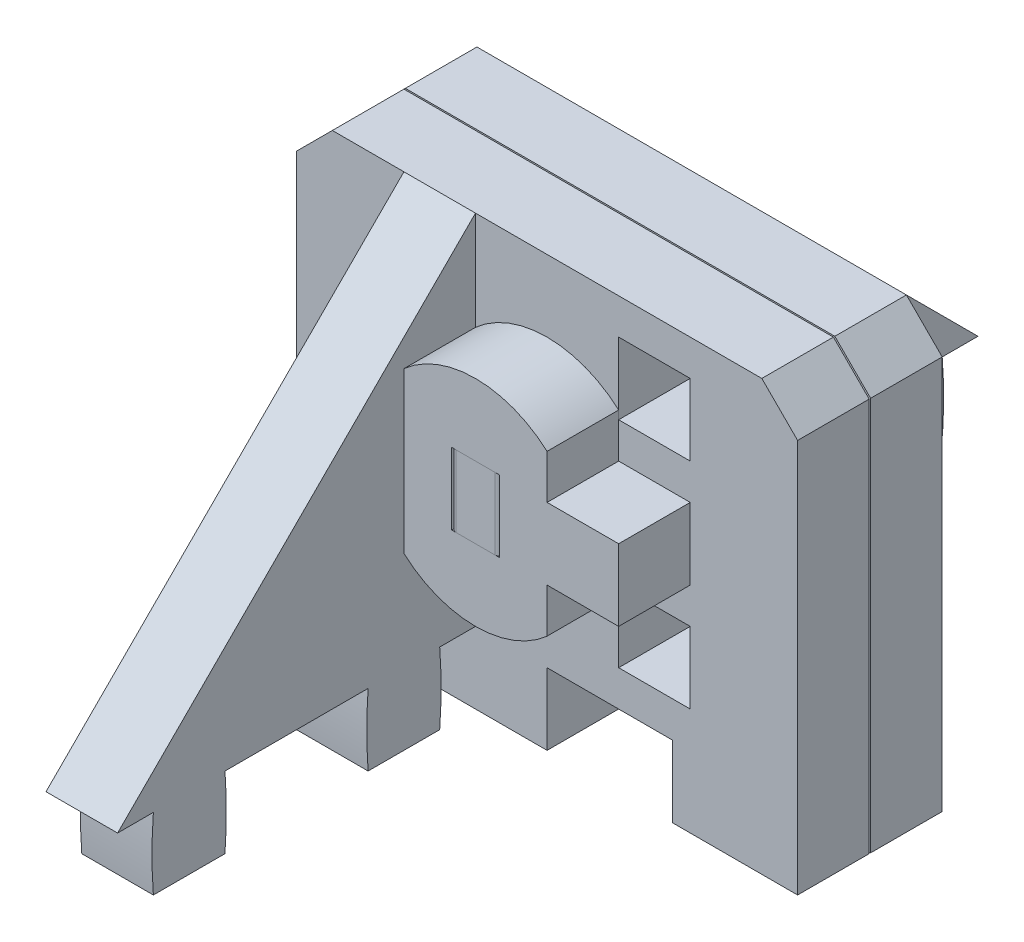
SolidWorks part; units mm, degrees
material "Faggio"
ref_plane "Piano frontale" through (0, 0, 0) normal (0, 0, 1) x (1, 0, 0)
ref_plane "Piano superiore" through (0, 0, 0) normal (0, 1, 0) x (1, 0, 0)
ref_plane "Piano destro" through (0, 0, 0) normal (1, 0, 0) x (0, 0, -1)
sketch "Schizzo1" plane through (0, 0, 0) normal (0, 0, 1) x (1, 0, 0)
  line L0 (-6, 6) -> (-6, 3)
  line L1 (-6, 3) -> (-3, 3)
  line L2 (-3, 3) -> (-3, 6)
  line L3 (-3, 6) -> (-6, 6)
  line L4 (-3, 3) -> (3, 3) construction
  line L5 (-6, -3) -> (-3, -3)
  line L6 (-6, -3) -> (-6, -6)
  line L7 (-6, -6) -> (-3, -6)
  line L8 (-3, -3) -> (-3, -6)
  line L17 (-1.5, -1.5) -> (1.5, -1.5) construction
  line L18 (-1.5, -1.5) -> (-1.5, 1.5) construction
  line L19 (-1.5, 1.5) -> (1.5, 1.5) construction
  line L20 (1.5, -1.5) -> (1.5, 1.5) construction
  line L21 (3, -3) -> (3, -6)
  line L22 (-10.5, 10.5) -> (-10.5, -10.5)
  line L23 (-10.5, -10.5) -> (10.5, -10.5)
  line L24 (10.5, -10.5) -> (10.5, 10.5)
  line L25 (10.5, 10.5) -> (-10.5, 10.5)
  line L26 (0, 10.5) -> (0, -10.5) construction
  line L27 (6, -6) -> (3, -6)
  line L28 (6, -3) -> (6, -6)
  line L29 (6, -3) -> (3, -3)
  line L30 (3, 6) -> (6, 6)
  line L31 (3, 3) -> (3, 6)
  line L32 (6, 3) -> (3, 3)
  line L33 (6, 6) -> (6, 3)
  line L35 (-3, 3) -> (-3, -3) construction
  circle A0 centre (0, 0) radius 2.1213
  point P30 (-3, 0)
extrude "Estrusione-Estrusione1" add sketch "Schizzo1" along normal blind 3
sketch "Schizzo6" plane through (0, 0, 3) normal (0, 0, 1) x (1, 0, 0)
  line L0 (-10.5, -7.5) -> (-5.25, -7.5)
  line L1 (-10.5, 10.5) -> (-10.5, -10.5) construction
  line L2 (-5.25, -7.5) -> (-5.25, -10.5)
  line L3 (-10.5, -10.5) -> (10.5, -10.5) construction
  line L4 (-5.25, -10.5) -> (0, -10.5) construction
  line L5 (0, -10.5) -> (0, -7.5)
  line L6 (0, -7.5) -> (5.25, -7.5)
  line L7 (5.25, -7.5) -> (5.25, -10.5)
  line L8 (5.25, -10.5) -> (0, -10.5)
  line L9 (-5.25, -10.5) -> (-10.5, -10.5)
  line L10 (-10.5, -10.5) -> (-10.5, -7.5)
  line L11 (5.25, -10.5) -> (10.5, -10.5) construction
  line L12 (10.5, -10.5) -> (10.5, 10.5) construction
extrude "Taglio-Estrusione1" cut sketch "Schizzo6" against normal up to next
sketch "Schizzo2" plane through (-6, 0, 0) normal (1, 0, 0) x (0, 0, -1)
  line L0 (-3, 6) -> (0, 6) construction
  line L1 (-3, 6) -> (0, 6) construction
  line L2 (-3, 6) -> (-3, 3) construction
  line L3 (0, 6) -> (0, 3) construction
  line L4 (-3, 6) -> (-3, 3)
  line L5 (-3, 3) -> (0, 3) construction
  line L6 (0, 10.5) -> (0, -7.5) construction
  line L7 (-3, 3) -> (0, 3) construction
  line L8 (0, 3) -> (0, 1.5)
  line L9 (0, -3) -> (-3, -3) construction
  line L10 (-3, -3) -> (-3, -6)
  line L11 (-3, -6) -> (0, -6) construction
  line L12 (0, -6) -> (0, -7.5)
  line L23 (15.75, -5.25) -> (2.25, 8.25)
  line L24 (2.25, 8.25) -> (0, 8.25)
  line L25 (0, 8.25) -> (0, 6)
  line L26 (0, -10.5) -> (0, 10.5) construction
  line L27 (0, -7.5) -> (9, 1.5) construction
  line L28 (15.75, -7.5) -> (13.5, -7.5)
  line L29 (15.75, -5.25) -> (15.75, -7.5)
  line L30 (1.5, -7.5) -> (0, -7.5)
  line L31 (1.5, -10.5) -> (1.5, -7.5) construction
  line L32 (4.5, -10.5) -> (1.5, -10.5)
  line L33 (4.5, -7.5) -> (4.5, -10.5) construction
  line L34 (10.5, -7.5) -> (4.5, -7.5)
  line L35 (10.5, -10.5) -> (10.5, -7.5) construction
  line L36 (13.5, -10.5) -> (10.5, -10.5)
  line L37 (13.5, -10.5) -> (13.5, -7.5) construction
  line L38 (-3, -10.5) -> (0, -10.5) construction
  line L39 (-1.5, 6.06) -> (-1.5, 6) construction
  line L40 (0, 1.5) -> (3, 1.5)
  line L41 (3, 1.5) -> (3, -1.5)
  line L42 (3, -1.5) -> (0, -1.5)
  line L43 (0, -1.5) -> (0, -3)
  arc A0 (-3, 6) -> (0, 6) centre (-1.5, -12.72) cw
  arc A1 (-3, 3) -> (0, 3) centre (-1.5, 21.72) ccw
  arc A2 (-3, -3) -> (0, -3) centre (-1.5, -21.72) cw
  arc A3 (-3, -6) -> (0, -6) centre (-1.5, 12.72) ccw
  arc A4 (1.5, -7.5) -> (1.5, -10.5) centre (20.22, -9) ccw
  arc A5 (4.5, -7.5) -> (4.5, -10.5) centre (-14.22, -9) cw
  arc A6 (10.5, -7.5) -> (10.5, -10.5) centre (29.22, -9) ccw
  arc A7 (13.5, -7.5) -> (13.5, -10.5) centre (-5.22, -9) cw
  point P58 (3, 0)
extrude "Estrusione-Estrusione2" add sketch "Schizzo2" along normal blind 3 separate body
sketch "Schizzo4" plane through (0, 0, 0) normal (0, 1, 0) x (0, 0, -1)
  line L0 (0, 1.5) -> (0, 2.5981)
  line L1 (-6.06, 1.5) -> (0, 1.5)
  line L2 (-6.06, 1.5) -> (-6.06, 1)
  line L3 (-6.06, -1.5) -> (0, -1.5)
  line L5 (0, 2.5981) -> (3, 2.5981)
  line L6 (3, 2.5981) -> (3, -2.5981)
  line L7 (3, -2.5981) -> (0, -2.5981)
  line L8 (0, -2.5981) -> (0, -1.5)
  line L11 (0, 1.5) -> (0, -1.5) construction
  line L12 (-6.06, 1) -> (-9.06, 1) construction
  line L13 (-9.06, 1) -> (-9.06, -1)
  line L14 (-9.06, -1) -> (-6.06, -1) construction
  line L15 (-6.06, -1) -> (-6.06, -1.5)
  line L16 (-7.56, 1.06) -> (-7.56, 1) construction
  line L17 (15.75, 3) -> (2.25, 3) construction
  line L19 (4.5, -2.5981) -> (7.5, -2.5981) construction
  line L20 (4.5, -2.5981) -> (4.5, 2.5981) construction
  line L21 (4.5, 2.5981) -> (7.5, 2.5981) construction
  line L22 (7.5, -2.5981) -> (7.5, 2.5981) construction
  arc A0 (-9.06, 1) -> (-6.06, 1) centre (-7.56, -17.72) cw
  arc A1 (-9.06, -1) -> (-6.06, -1) centre (-7.56, 17.72) ccw
  circle A2 centre (6, 0) radius 3 construction
  point P1 (3, 0)
extrude "Estrusione-Estrusione4" add sketch "Schizzo4" along normal mid plane 3 separate body
sketch "Schizzo8" plane through (10.5, 0, 0) normal (1, 0, 0) x (0, 0, -1)
  line L0 (0, 7.5) -> (18, -10.5)
  line L1 (-3, 10.5) -> (0, 10.5)
  line L2 (0, 10.5) -> (18, -7.5)
  line L3 (18, -7.5) -> (18, -10.5)
  line L4 (15.75, -5.25) -> (2.25, 8.25) construction
  line L5 (-3, -10.5) -> (0, -10.5) construction
  line L6 (0, 7.5) -> (-3, 7.5)
  line L7 (0, 8.25) -> (0, 6) construction
  line L8 (-3, -10.5) -> (-3, 10.5) construction
  line L9 (-3, 7.5) -> (-3, 10.5)
  line L10 (0, -10.5) -> (0, 10.5) construction
extrude "Taglio-Estrusione2" cut sketch "Schizzo8" against normal through all both and the other way through all
chamfer "Smusso1" distance 1.5 angle 45 2 edges at (-10.5, 7.5, 1.5) (10.5, 7.5, 1.5)
sketch "Schizzo5" plane through (0, 0, 6.06) normal (0, 0, 1) x (1, 0, 0)
  line L1 (1, -1.5) -> (-1, -1.5)
  line L2 (1, -1.5) -> (1, 1.5)
  line L3 (1, 1.5) -> (-1, 1.5)
  line L4 (-1, -1.5) -> (-1, 1.5)
  line L6 (-3, -3.3541) -> (-3, -1.5)
  line L7 (3, -3.3541) -> (3, -1.5)
  line L9 (-1, -1.5) -> (1, -1.5) construction
  line L10 (-3, 1.5) -> (-6, 1.5)
  line L11 (-6, 1.5) -> (-6, -1.5)
  line L12 (-6, -1.5) -> (-3, -1.5)
  line L13 (3, 1.5) -> (6, 1.5)
  line L14 (6, 1.5) -> (6, -1.5)
  line L15 (6, -1.5) -> (3, -1.5)
  line L16 (-6, 6) -> (-6, 3) construction
  line L17 (-3, 1.5) -> (-3, 3.3541)
  line L18 (3, 1.5) -> (3, 3.3541)
  arc A0 (-3, -3.3541) -> (3, -3.3541) centre (0, 0) ccw
  arc A1 (3, 3.3541) -> (-3, 3.3541) centre (0, 0) ccw
  point P22 (0, 1.5)
  point P27 (-6, 0)
extrude "Estrusione-Estrusione5" add sketch "Schizzo5" along normal blind 3 separate body
ref_plane "Piano1" through (0, 0, 3.03) normal (0, 0, -1) x (-1, 0, 0)
mirror "Specchia1" about plane through (0, 0, 3.03) normal (0, 0, -1) of bodies 110 108 101 102
fillet "Raccordo1" radius 0.2 2 edges at (1, 0, 9.06) (-1, 0, 9.06)
fillet "Raccordo2" radius 0.2 8 edges at (-4.5, -10.5, -13.5) (-4.5, -10.5, -10.5) (-4.5, -10.5, -4.5) (-4.5, -10.5, -1.5) (-4.5, -6, 3) (-4.5, 3, 3) (-4.5, 6, 3) (-4.5, -3, 3)
equation "\"t\"= 3mm'thickness"
equation "\"D1@Schizzo4\"=\"t\""
equation "\"D2@Schizzo4\"=2*\"t\"+\"i\""
equation "\"D3@Schizzo4\"=\"t\"*2/3"
equation "\"D1@Estrusione-Estrusione4\" = \"t\""
equation "\"D1@Schizzo5\"=\"t\"*3"
equation "\"D1@Estrusione-Estrusione5\"=\"t\""
equation "\"D2@Schizzo1\"=\"t\""
equation "\"D1@Schizzo1\"=\"t\""
equation "\"D3@Schizzo1\"=\"t\"*7"
equation "\"D2@Schizzo5\"=\"t\"*2"
equation "\"D1@Schizzo6\"=\"t\""
equation "\"i\"= 0.06mm'interference"
equation "\"D1@Schizzo2\"=\"i\""
equation "\"D5@Schizzo4\"=\"i\""
equation "\"D1@Smusso1\"=\"t\"/2"
